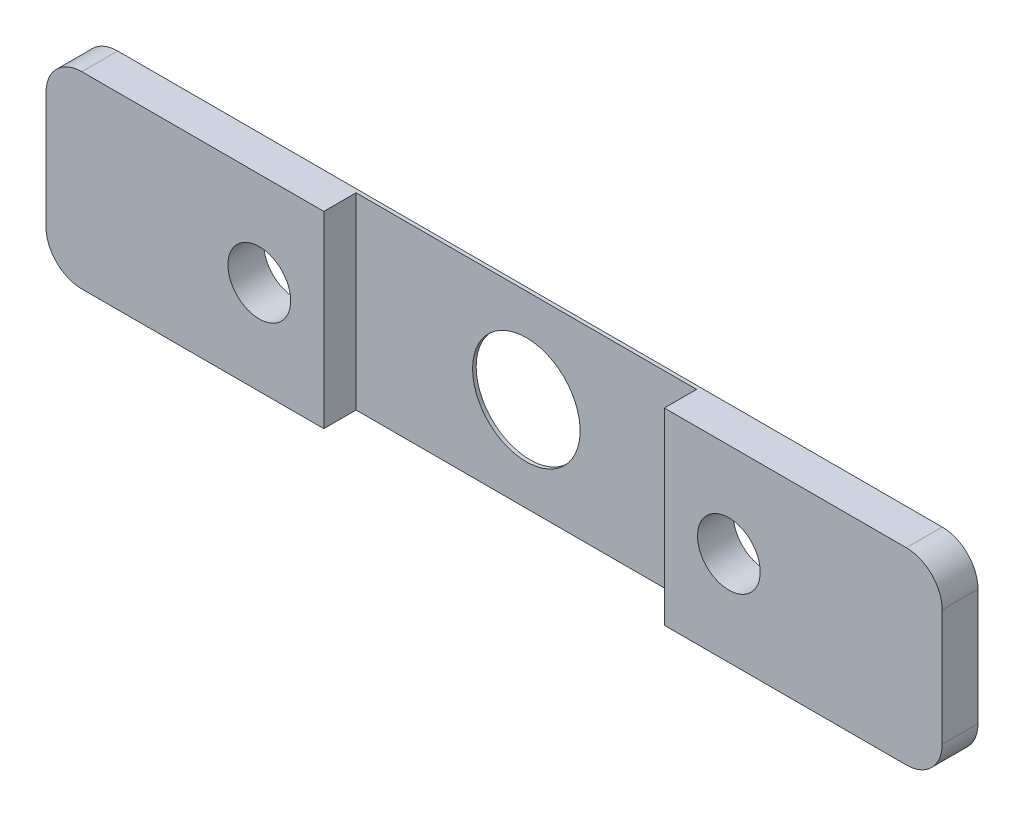
SolidWorks part; units mm, degrees
ref_plane "正面" through (0, 0, 0) normal (0, 0, 1) x (1, 0, 0)
ref_plane "平面" through (0, 0, 0) normal (0, 1, 0) x (1, 0, 0)
ref_plane "右側面" through (0, 0, 0) normal (1, 0, 0) x (0, 0, -1)
sketch "ｽｹｯﾁ1" plane through (0, 0, 0) normal (0, 0, 1) x (1, 0, 0)
  line L0 (-25, 0) -> (25, 0) construction
  line L1 (-25, -5.25) -> (25, -5.25)
  line L2 (-25, -5.25) -> (-25, 5.25)
  line L3 (-25, 5.25) -> (25, 5.25)
  line L4 (25, -5.25) -> (25, 5.25)
  line L5 (-25, -5.25) -> (25, 5.25) construction
  line L6 (-25, 5.25) -> (25, -5.25) construction
  circle A3 centre (13.1, 0) radius 1.75
  circle A4 centre (-13.1, 0) radius 1.75
  point P0 (0, 0)
  point P15 (0, 0)
  dimension "D1" = 50
  dimension "D2" = 10.5
  dimension "D5" = 3.5
  dimension "D6" = 3.5
  dimension "D3" = 13.1
  dimension "D4" = 13.1
extrude "ﾎﾞｽ - 押し出し1" add sketch "ｽｹｯﾁ1" along normal blind 2
fillet "ﾌｨﾚｯﾄ1" radius 2 4 edges at (-25, 5.25, 1) (-25, -5.25, 1) (25, -5.25, 1) (25, 5.25, 1)
sketch "ｽｹｯﾁ2" plane through (0, 0, 2) normal (0, 0, 1) x (1, 0, 0)
  line L0 (-25, 0) -> (25, 0) construction
  line L1 (-25, 3.25) -> (-25, -3.25) construction
  line L2 (25, -3.25) -> (25, 3.25) construction
  line L3 (0, 5.25) -> (0, -5.25) construction
  line L4 (23, 5.25) -> (-23, 5.25) construction
  line L5 (-23, -5.25) -> (23, -5.25) construction
  line L7 (-9.5, -5.25) -> (9.5, -5.25)
  line L8 (-9.5, -5.25) -> (-9.5, 5.25)
  line L9 (-9.5, 5.25) -> (9.5, 5.25)
  line L10 (9.5, -5.25) -> (9.5, 5.25)
  line L11 (-9.5, -5.25) -> (9.5, 5.25) construction
  line L12 (-9.5, 5.25) -> (9.5, -5.25) construction
  point P12 (0, 0)
  dimension "D1" = 19
extrude "ｶｯﾄ - 押し出し1" cut sketch "ｽｹｯﾁ2" against normal blind 1.8
sketch "ｽｹｯﾁ3" plane through (0, 0, 0) normal (0, 0, -1) x (-1, 0, 0)
  line L0 (25, 0) -> (-25, 0) construction
  line L1 (25, 3.25) -> (25, -3.25) construction
  line L2 (-25, -3.25) -> (-25, 3.25) construction
  line L3 (0, -5.25) -> (0, 5.25) construction
  line L4 (23, -5.25) -> (-23, -5.25) construction
  line L5 (-23, 5.25) -> (23, 5.25) construction
  circle A0 centre (0, 0) radius 3
  dimension "D1" = 6
extrude "ｶｯﾄ - 押し出し2" cut sketch "ｽｹｯﾁ3" against normal through all
